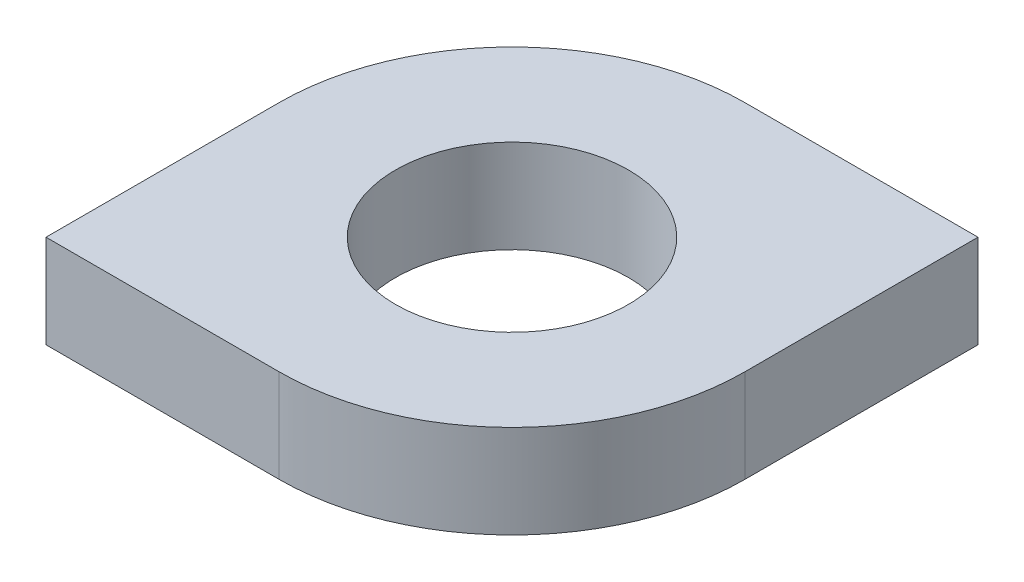
SolidWorks part; units mm, degrees
ref_plane "Спереди" through (0, 0, 0) normal (0, 0, 1) x (1, 0, 0)
ref_plane "Сверху" through (0, 0, 0) normal (0, 1, 0) x (1, 0, 0)
ref_plane "Справа" through (0, 0, 0) normal (1, 0, 0) x (0, 0, -1)
sketch "Эскиз1" plane through (0, 0, 0) normal (0, 1, 0) x (1, 0, 0)
  line L0 (0, 0) -> (10, 0)
  line L1 (20, 10) -> (20, 20)
  line L2 (20, 20) -> (10, 20)
  line L3 (0, 10) -> (0, 0)
  arc A0 (10, 20) -> (0, 10) centre (10, 10) ccw
  arc A1 (10, 0) -> (20, 10) centre (10, 10) ccw
  dimension "D1" = 10
extrude "Бобышка-Вытянуть1" add sketch "Эскиз1" along normal blind 4
sketch "Эскиз2" plane through (0, 4, 0) normal (0, 1, 0) x (1, 0, 0)
  circle A0 centre (10, 10) radius 5
extrude "Вырез-Вытянуть1" cut sketch "Эскиз2" against normal through all
